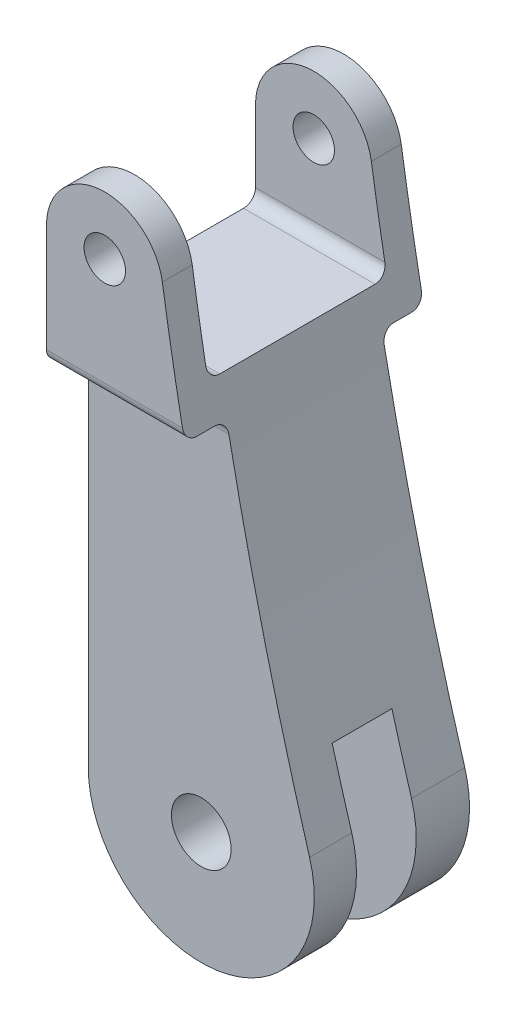
SolidWorks part; units mm, degrees
ref_plane "前视基准面" through (0, 0, 0) normal (0, 0, 1) x (1, 0, 0)
ref_plane "上视基准面" through (0, 0, 0) normal (0, 1, 0) x (1, 0, 0)
ref_plane "右视基准面" through (0, 0, 0) normal (1, 0, 0) x (0, 0, -1)
sketch "草图1" plane through (0, 0, 0) normal (0, 0, 1) x (1, 0, 0)
  line L0 (-94.6123, 0) -> (-94.6123, 410)
  line L1 (0, 0) -> (90.6549, 27.0771) construction
  line L2 (0, 0) -> (-94.6123, 0) construction
  arc A0 (-94.6123, 0) -> (90.6549, 27.0771) centre (0, 0) ccw
  circle A1 centre (0, 0) radius 25
  arc A2 (2.4076, 417.5019) -> (-94.6123, 410) centre (-45.8123, 410) ccw
  circle A3 centre (-45.8123, 410) radius 17.35
  arc A4 (2.4076, 417.5019) -> (90.6549, 27.0771) centre (2914.7933, 870.5997) ccw
  dimension "D1" = 34.7
  dimension "D2" = 50
  dimension "D4" = 48.8
  dimension "D3" = 410
  dimension "D5" = 163.37
extrude "凸台-拉伸1" add sketch "草图1" along normal mid plane 200
sketch "草图2" plane through (-94.6123, 0, 0) normal (-1, 0, 0) x (0, 0, 1)
  line L0 (0, 0) -> (0, 503.712) construction
  line L1 (-100, 410) -> (-100, 0) construction
  line L2 (-75, 340) -> (75, 340)
  line L3 (-75, 340) -> (-75, 503.3501)
  line L4 (-75, 503.3501) -> (75, 503.3501)
  line L5 (75, 340) -> (75, 503.3501)
  line L6 (-75, 340) -> (75, 503.3501) construction
  line L7 (-75, 503.3501) -> (75, 340) construction
  line L8 (-165.7215, 310) -> (-65, 310)
  line L9 (-165.7215, 310) -> (-165.7215, -138.4954)
  line L10 (-165.7215, -138.4954) -> (-65, -138.4954)
  line L11 (-65, 310) -> (-65, -138.4954)
  line L13 (100, 0) -> (-100, 0) construction
  line L14 (165.7215, 310) -> (165.7215, -138.4954)
  line L15 (65, 310) -> (65, -138.4954)
  line L16 (165.7215, 310) -> (65, 310)
  line L17 (165.7215, -138.4954) -> (65, -138.4954)
  point P3 (0, 421.6751)
  dimension "D1" = 25
  dimension "D2" = 150
  dimension "D3" = 340
  dimension "D4" = 310
  dimension "D5" = 35
extrude "切除-拉伸1" cut sketch "草图2" against normal blind 310
sketch "草图3" plane through (-94.6123, 0, 0) normal (-1, 0, 0) x (0, 0, 1)
  line L0 (-75, 340) -> (75, 340) construction
  line L1 (-20.3328, 84) -> (29.6672, 84)
  line L2 (-20.3328, 84) -> (-20.3328, -274.5858)
  line L3 (-20.3328, -274.5858) -> (29.6672, -274.5858)
  line L4 (29.6672, 84) -> (29.6672, -274.5858)
  line L5 (-20.3328, 84) -> (29.6672, -274.5858) construction
  line L6 (-20.3328, -274.5858) -> (29.6672, 84) construction
  point P0 (4.6672, -95.2929)
  dimension "D1" = 256
  dimension "D2" = 50
extrude "切除-拉伸2" cut sketch "草图3" against normal blind 310
fillet "圆角1" radius 10 6 edges at (-36.7177, 310, 65) (-36.7177, 310, -65) (-36.7177, 310, -100) (-36.7177, 310, 100) (-39.5432, 340, -75) (-39.5432, 340, 75)
